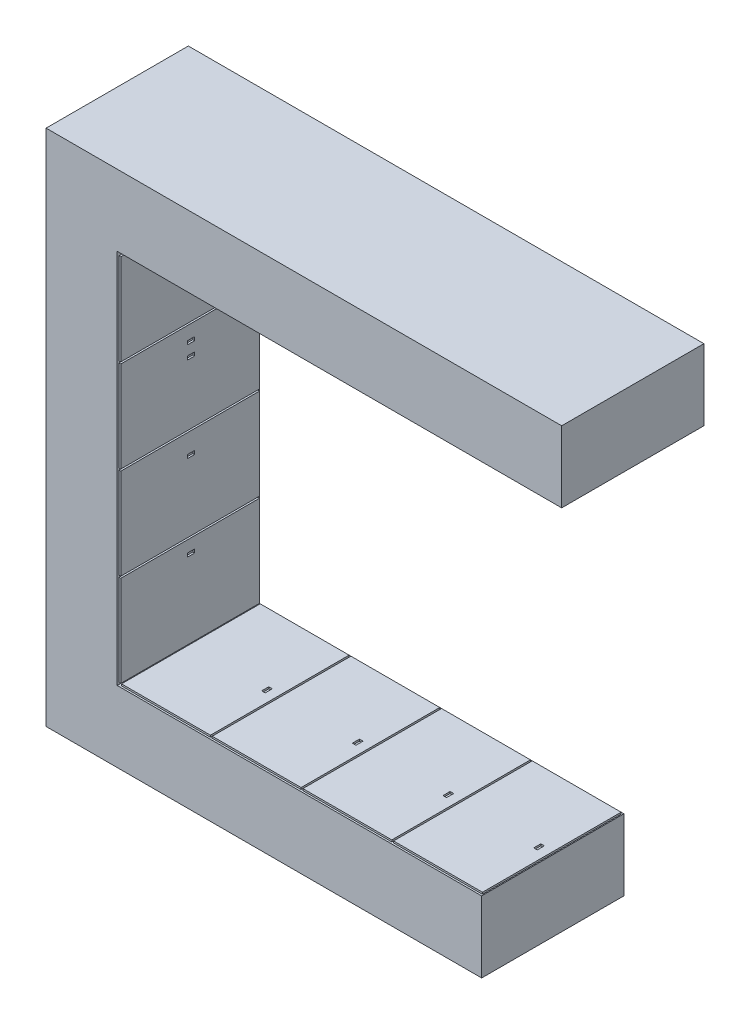
SolidWorks part; units mm, degrees
ref_plane "Front Plane" through (0, 0, 0) normal (0, 0, 1) x (1, 0, 0)
ref_plane "Top Plane" through (0, 0, 0) normal (0, 1, 0) x (1, 0, 0)
ref_plane "Right Plane" through (0, 0, 0) normal (1, 0, 0) x (0, 0, -1)
sketch "Sketch1" plane through (0, 0, 0) normal (0, 0, 1) x (1, 0, 0)
  line L0 (2763.062, 160) -> (-136.938, 160)
  line L1 (-136.938, 160) -> (-136.938, -2755)
  line L2 (-136.938, -2755) -> (2313.062, -2755)
  line L3 (2313.062, -2755) -> (2313.062, -2355)
  line L4 (2313.062, -2355) -> (263.062, -2355)
  line L5 (263.062, -2355) -> (263.062, -240)
  line L6 (263.062, -240) -> (2763.062, -240)
  line L7 (2763.062, -240) -> (2763.062, 160)
  dimension "D1" = 400
  dimension "D2" = 2915
  dimension "D3" = 400
  dimension "D4" = 400
  dimension "D5" = 2450
  dimension "D6" = 2900
extrude "Boss-Extrude1" add sketch "Sketch1" along normal blind 800
sketch "Sketch2" plane through (0, -2355, 0) normal (0, 1, 0) x (1, 0, 0)
  line L0 (787.5401, -10) -> (1287.5401, -10)
  line L1 (277.5401, -10) -> (777.5401, -10)
  line L2 (277.5401, -10) -> (277.5401, -790)
  line L3 (277.5401, -790) -> (777.5401, -790)
  line L4 (777.5401, -10) -> (777.5401, -790)
  line L5 (705.6277, -390) -> (725.6277, -390)
  line L6 (705.6277, -390) -> (705.6277, -430)
  line L7 (705.6277, -430) -> (725.6277, -430)
  line L8 (725.6277, -390) -> (725.6277, -430)
  line L9 (787.5401, -10) -> (787.5401, -790)
  line L10 (787.5401, -790) -> (1287.5401, -790)
  line L11 (1235.6277, -390) -> (1235.6277, -430)
  line L12 (1215.6277, -390) -> (1235.6277, -390)
  line L13 (1215.6277, -430) -> (1235.6277, -430)
  line L14 (1215.6277, -390) -> (1215.6277, -430)
  line L15 (1287.5401, -10) -> (1287.5401, -790)
  line L16 (1297.5401, -10) -> (1797.5401, -10)
  line L17 (1297.5401, -10) -> (1297.5401, -790)
  line L18 (1297.5401, -790) -> (1797.5401, -790)
  line L19 (1745.6277, -390) -> (1745.6277, -430)
  line L20 (1725.6277, -390) -> (1745.6277, -390)
  line L21 (1725.6277, -430) -> (1745.6277, -430)
  line L22 (1725.6277, -390) -> (1725.6277, -430)
  line L23 (1797.5401, -10) -> (1797.5401, -790)
  line L24 (1807.5401, -10) -> (2307.5401, -10)
  line L25 (1807.5401, -10) -> (1807.5401, -790)
  line L26 (1807.5401, -790) -> (2307.5401, -790)
  line L27 (2255.6277, -390) -> (2255.6277, -430)
  line L28 (2235.6277, -390) -> (2255.6277, -390)
  line L29 (2235.6277, -430) -> (2255.6277, -430)
  line L30 (2235.6277, -390) -> (2235.6277, -430)
  line L31 (2307.5401, -10) -> (2307.5401, -790)
  line L32 (2313.062, 0) -> (263.062, 0) construction
  line L33 (2313.062, -800) -> (263.062, -800) construction
  dimension "D1" = 500
  dimension "D3" = 360
  dimension "D4" = 4
  dimension "D5" = 20
  dimension "D6" = 40
  dimension "D7" = 10
  dimension "D8" = 10
  dimension "D9" = 10
extrude "Boss-Extrude2" add sketch "Sketch2" along normal blind 10
sketch "Sketch3" plane through (263.062, 0, 0) normal (1, 0, 0) x (0, 0, -1)
  line L0 (-10, -1823) -> (-790, -1823)
  line L1 (-10, -2345) -> (-790, -2345)
  line L2 (-10, -2345) -> (-10, -1833)
  line L3 (-10, -1833) -> (-790, -1833)
  line L4 (-790, -2345) -> (-790, -1833)
  line L5 (-415, -1897.5884) -> (-375, -1897.5884)
  line L6 (-415, -1897.5884) -> (-415, -1917.5884)
  line L7 (-415, -1917.5884) -> (-375, -1917.5884)
  line L8 (-375, -1897.5884) -> (-375, -1917.5884)
  line L9 (-10, -1823) -> (-10, -1311)
  line L10 (-10, -1311) -> (-790, -1311)
  line L11 (-790, -1823) -> (-790, -1311)
  line L12 (-415, -1417.5884) -> (-375, -1417.5884)
  line L13 (-415, -1417.5884) -> (-415, -1437.5884)
  line L14 (-415, -1437.5884) -> (-375, -1437.5884)
  line L15 (-375, -1417.5884) -> (-375, -1437.5884)
  line L16 (-10, -1301) -> (-790, -1301)
  line L17 (-10, -1301) -> (-10, -789)
  line L18 (-10, -789) -> (-790, -789)
  line L19 (-790, -1301) -> (-790, -789)
  line L20 (-415, -937.5884) -> (-375, -937.5884)
  line L21 (-415, -937.5884) -> (-415, -957.5884)
  line L22 (-415, -957.5884) -> (-375, -957.5884)
  line L23 (-375, -937.5884) -> (-375, -957.5884)
  line L24 (-10, -779) -> (-790, -779)
  line L25 (-10, -779) -> (-10, -267)
  line L26 (-10, -267) -> (-790, -267)
  line L27 (-790, -779) -> (-790, -267)
  line L28 (-415, -863.2446) -> (-375, -863.2446)
  line L29 (-415, -863.2446) -> (-415, -883.2446)
  line L30 (-415, -883.2446) -> (-375, -883.2446)
  line L31 (-375, -863.2446) -> (-375, -883.2446)
  line L33 (-800, -2355) -> (0, -2355) construction
  line L34 (-800, -2355) -> (-800, -240) construction
  line L35 (0, -2355) -> (0, -240) construction
  dimension "D1" = 512
  dimension "D2" = 40
  dimension "D3" = 20
  dimension "D4" = 375
  dimension "D6" = 10
  dimension "D7" = 10
  dimension "D5" = 512
  dimension "D8" = 512
  dimension "D9" = 512
  dimension "D10" = 10
  dimension "D11" = 10
  dimension "D12" = 10
  dimension "D13" = 10
extrude "Boss-Extrude3" add sketch "Sketch3" along normal blind 10 contours L11 L0 L9 L10 L12 L15 L14 L13 | L19 L16 L17 L18 L20 L23 L22 L21 | L4 L1 L2 L3 L5 L8 L7 L6 | L27 L24 L25 L26 L28 L31 L30 L29
sketch "Sketch4" plane through (0, -240, 0) normal (0, -1, 0) x (1, 0, 0)
  line L0 (-136.938, 0) -> (2313.062, 0) construction
  line L1 (296.4309, 790) -> (776.4309, 790)
  line L2 (296.4309, 790) -> (296.4309, 10)
  line L3 (296.4309, 10) -> (776.4309, 10)
  line L4 (776.4309, 790) -> (776.4309, 10)
  line L5 (786.4309, 790) -> (1266.4309, 790)
  line L6 (742.986, 484) -> (722.986, 484)
  line L7 (742.986, 484) -> (742.986, 444)
  line L8 (742.986, 444) -> (722.986, 444)
  line L9 (722.986, 484) -> (722.986, 444)
  line L10 (786.4309, 790) -> (786.4309, 10)
  line L11 (1266.4309, 790) -> (1266.4309, 10)
  line L12 (1232.986, 484) -> (1212.986, 484)
  line L13 (1232.986, 484) -> (1232.986, 444)
  line L14 (1232.986, 444) -> (1212.986, 444)
  line L15 (1212.986, 484) -> (1212.986, 444)
  line L16 (786.4309, 10) -> (1266.4309, 10)
  line L17 (1276.4309, 790) -> (1756.4309, 790)
  line L18 (1276.4309, 790) -> (1276.4309, 10)
  line L19 (1756.4309, 790) -> (1756.4309, 10)
  line L20 (1722.986, 484) -> (1702.986, 484)
  line L21 (1722.986, 484) -> (1722.986, 444)
  line L22 (1722.986, 444) -> (1702.986, 444)
  line L23 (1702.986, 484) -> (1702.986, 444)
  line L24 (1276.4309, 10) -> (1756.4309, 10)
  line L25 (1766.4309, 790) -> (2246.4309, 790)
  line L26 (1766.4309, 790) -> (1766.4309, 10)
  line L27 (2246.4309, 790) -> (2246.4309, 10)
  line L28 (2212.986, 484) -> (2192.986, 484)
  line L29 (2212.986, 484) -> (2212.986, 444)
  line L30 (2212.986, 444) -> (2192.986, 444)
  line L31 (2192.986, 484) -> (2192.986, 444)
  line L32 (1766.4309, 10) -> (2246.4309, 10)
  line L33 (2256.4309, 790) -> (2736.4309, 790)
  line L34 (2256.4309, 790) -> (2256.4309, 10)
  line L35 (2736.4309, 790) -> (2736.4309, 10)
  line L36 (2702.986, 484) -> (2682.986, 484)
  line L37 (2702.986, 484) -> (2702.986, 444)
  line L38 (2702.986, 444) -> (2682.986, 444)
  line L39 (2682.986, 484) -> (2682.986, 444)
  line L40 (2256.4309, 10) -> (2736.4309, 10)
  line L41 (263.062, 800) -> (2763.062, 800) construction
  dimension "D1" = 10
  dimension "D2" = 10
  dimension "D3" = 40
  dimension "D4" = 20
  dimension "D5" = 306
  dimension "D7" = 480
  dimension "D8" = 10
  dimension "D6" = 5
extrude "Boss-Extrude4" add sketch "Sketch4" along normal blind 10 contours L4 L1 L2 L3 L9 L6 L7 L8 | L18 L24 L19 L17 L23 L20 L21 L22 | L26 L32 L27 L25 L31 L28 L29 L30 | L34 L40 L35 L33 L39 L36 L37 L38 | L10 L16 L11 L5 L15 L12 L13 L14
equation "\"Ab\"=10"
equation "\"D12@Sketch3\"=\"Ab\""
equation "\"D10@Sketch3\"=\"Ab\""
equation "\"D11@Sketch3\"=\"Ab\""
equation "\"D13@Sketch3\"=\"Ab\""
equation "\"Ac\"=512"
equation "\"D1@Sketch3\"=\"Ac\""
equation "\"D5@Sketch3\"=\"Ac\""
equation "\"D8@Sketch3\"=\"Ac\""
equation "\"D9@Sketch3\"=\"Ac\""
equation "\"D7@Sketch2\"=\"Ab\""
equation "\"D8@Sketch2\"=\"Ab\""
equation "\"D6@Sketch3\"=\"Ab\""
equation "\"D7@Sketch3\"=\"Ab\""
equation "\"D2@Sketch4\"=\"Ab\""
equation "\"D1@Sketch4\"=\"Ab\""
equation "\"D8@Sketch4\"=\"Ab\""
